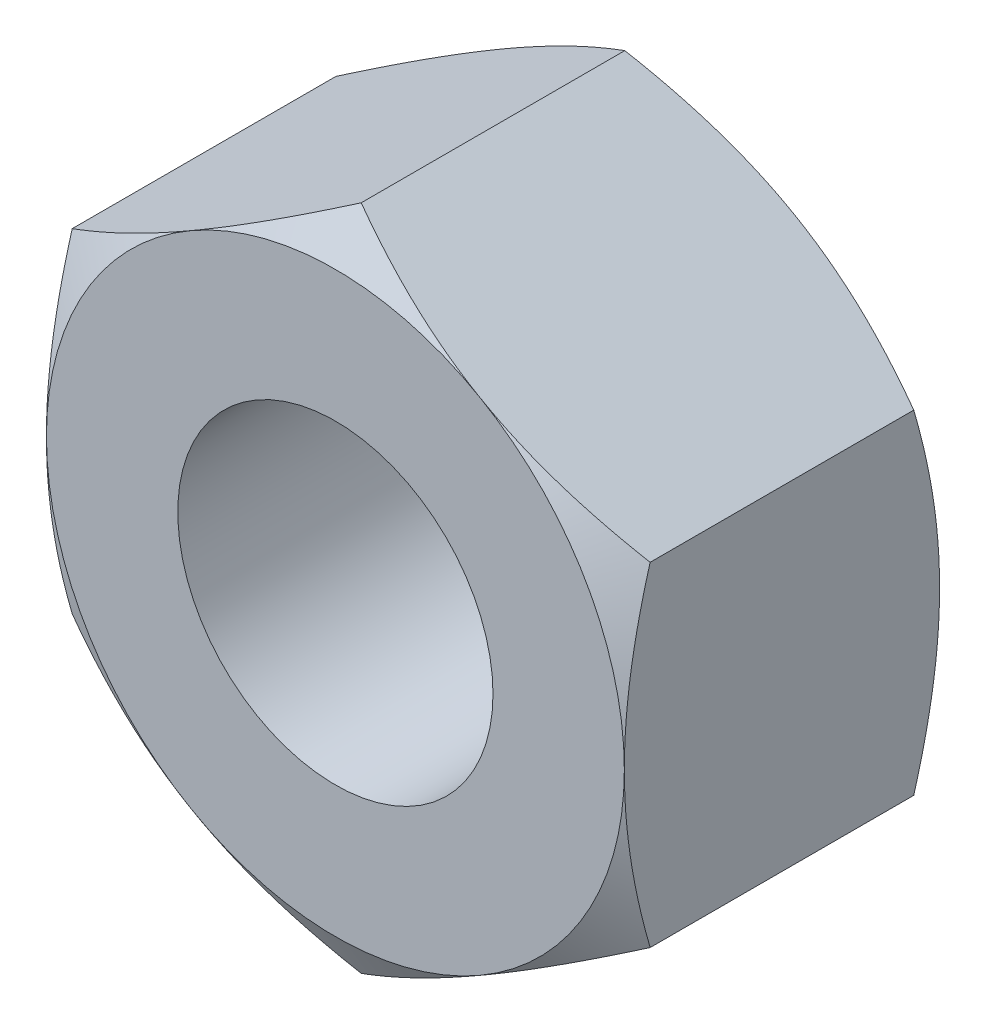
SolidWorks part; units mm, degrees
ref_plane "Plan de face" through (0, 0, 0) normal (0, 0, 1) x (1, 0, 0)
ref_plane "Plan de dessus" through (0, 0, 0) normal (0, 1, 0) x (1, 0, 0)
ref_plane "Plan de droite" through (0, 0, 0) normal (1, 0, 0) x (0, 0, -1)
sketch "Esquisse1" plane through (0, 0, 0) normal (0, 0, 1) x (1, 0, 0)
  line L1 (0, 3.1754) -> (-2.75, 1.5877)
  line L2 (-2.75, 1.5877) -> (-2.75, -1.5877)
  line L3 (-2.75, -1.5877) -> (0, -3.1754)
  line L4 (0, -3.1754) -> (2.75, -1.5877)
  line L5 (2.75, -1.5877) -> (2.75, 1.5877)
  line L6 (2.75, 1.5877) -> (0, 3.1754)
  circle A0 centre (0, 0) radius 2.75 construction
  dimension "D1" = 5.5
extrude "Boss.-Extru.1" add sketch "Esquisse1" along normal blind 3
sketch "Esquisse2" plane through (0, 0, 3) normal (0, 0, 1) x (1, 0, 0)
  circle A0 centre (0, 0) radius 1.5
  dimension "D1" = 3
extrude "Enlèv. mat.-Extru.1" cut sketch "Esquisse2" against normal up to next
sketch "Esquisse4" plane through (0, 0, 0) normal (0, 1, 0) x (1, 0, 0)
  line L0 (-5.3481, -1.5) -> (-1.0179, 1)
  line L1 (0, 0) -> (-2.75, 0) construction
  line L3 (-5.3481, -1.5) -> (-1.0179, -4)
  line L4 (-1.0179, 1) -> (-6.3481, 1)
  line L5 (-6.3481, 1) -> (-6.3481, -4)
  line L6 (-6.3481, -4) -> (-1.0179, -4)
  line L7 (0, 0) -> (0, -3) construction
  dimension "D1" = 1
  dimension "D2" = 1
  dimension "D3" = 30
revolve "Enlèvement de matière-Révolution8" cut sketch "Esquisse4" angle 360 about L7
